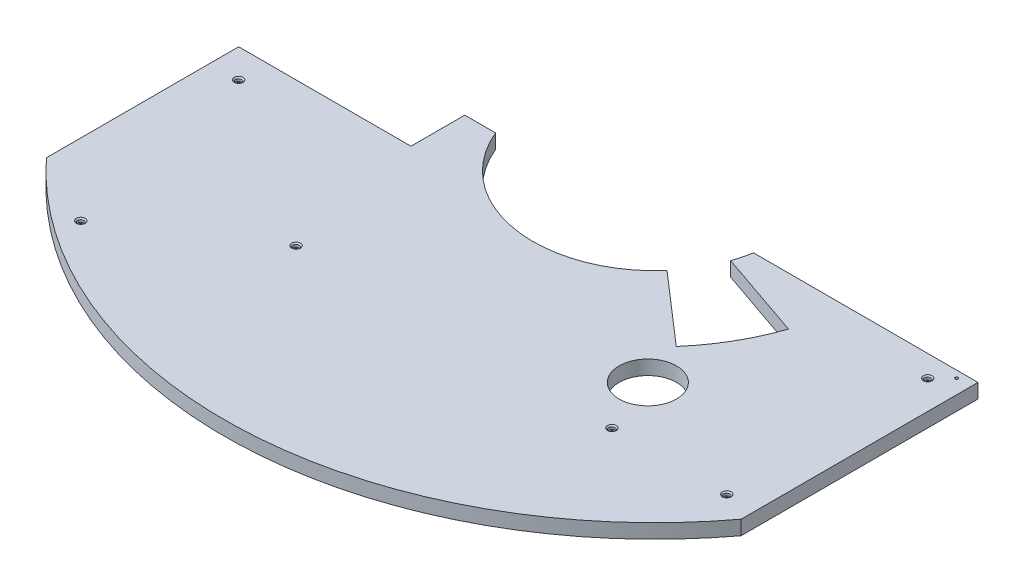
SolidWorks part; units mm, degrees
ref_plane "Front" through (0, 0, 0) normal (0, 0, 1) x (1, 0, 0)
ref_plane "Top" through (0, 0, 0) normal (0, 1, 0) x (1, 0, 0)
ref_plane "Right" through (0, 0, 0) normal (1, 0, 0) x (0, 0, -1)
sketch "Sketch2" plane through (0, 0, 0) normal (0, 1, 0) x (1, 0, 0)
  line L1 (-406.5798, 524.4548) -> (1600.0202, 524.4548)
  line L2 (-406.5798, 524.4548) -> (-406.5798, -237.5452)
  line L3 (-406.5798, -237.5452) -> (1600.0202, -237.5452)
  line L4 (1600.0202, 524.4548) -> (1600.0202, -237.5452)
  dimension "D1" = 762
  dimension "D2" = 2006.6
extrude "Boss-Extrude1" add sketch "Sketch2" along normal blind 25.4
sketch "Sketch102" plane through (0, 25.4, 0) normal (0, 1, 0) x (1, 0, 0)
  line L1 (1600.0202, -237.5452) -> (1600.0202, 524.4548) construction
  line L3 (1600.0202, 524.4548) -> (-406.5798, 524.4548) construction
  line L4 (-101.7798, 851.1379) -> (-101.7798, -458.2879) construction
  line L6 (152.2202, 524.4548) -> (439.7646, 274.4963)
  line L7 (512.4628, 400.4133) -> (152.2202, 524.4548)
  line L9 (-406.5798, 524.4548) -> (1600.0202, 524.4548)
  line L10 (-406.5798, 524.4548) -> (-406.5798, 67.2548)
  line L11 (-406.5798, 67.2548) -> (1600.0202, 67.2548)
  line L12 (1600.0202, 524.4548) -> (1600.0202, 67.2548)
  circle A0 centre (152.2202, 524.4548) radius 215.9
  arc A1 (439.7646, 274.4963) -> (512.4628, 400.4133) centre (152.2202, 524.4548) ccw
  circle A2 centre (469.7202, 194.2548) radius 50.8
  circle A3 centre (152.2202, 524.4548) radius 762
  dimension "D3" = 558.8
  dimension "D4" = 431.8
  dimension "D9" = 101.6
  dimension "D5" = 254
  dimension "D6" = 41
  dimension "D7" = 22
  dimension "D8" = 381
  dimension "D10" = 330.2
  dimension "D11" = 317.5
  dimension "D12" = 457.2
sketch "Sketch113" plane through (0, 25.4, 0) normal (0, 1, 0) x (1, 0, 0)
  line L0 (761.8202, 67.2548) -> (761.8202, 807.6635) construction
  line L1 (-406.5798, 67.2548) -> (1600.0202, 67.2548) construction
  line L2 (-406.5798, 524.4548) -> (1600.0202, 524.4548) construction
  line L3 (736.4202, 807.6635) -> (736.4202, -32.6479) construction
  line L4 (807.5255, 473.6548) -> (-505.9709, 473.6548) construction
  circle A0 centre (152.2202, 524.4548) radius 762 construction
  dimension "D1" = 25.4
  dimension "D2" = 50.8
sketch "Sketch120" plane through (0, 25.4, 0) normal (0, 1, 0) x (1, 0, 0)
  line L0 (-406.5798, 524.4548) -> (1600.0202, 524.4548) construction
  line L1 (364.7319, 486.3548) -> (761.8202, 486.3548)
  line L2 (761.8202, 67.2548) -> (761.8202, 807.6635) construction
  line L3 (761.8202, 486.3548) -> (761.8202, 524.4548)
  line L4 (761.8202, 524.4548) -> (368.1202, 524.4548)
  arc A0 (368.1202, 524.4548) -> (364.7319, 486.3548) centre (152.2202, 524.4548) cw
  circle A1 centre (152.2202, 524.4548) radius 215.9 construction
  dimension "D1" = 38.1
extrude "Cut-Extrude18" cut sketch "Sketch120" against normal through all
hole_wizard "1/4-20 Tapped Hole1" positions "Sketch122" profile "Sketch121" tap size "1/4-20" standard "ANSI Inch" end condition through all
sketch "Sketch122" plane through (0, 25.4, 0) normal (0, 1, 0) x (1, 0, 0)
  line L0 (736.4202, 807.6635) -> (736.4202, -32.6479) construction
  point P0 (736.4202, 473.9488)
sketch "Sketch121" plane through (736.4202, 25.4, -473.9488) normal (1, 0, 0) x (0, 0, 1)
  line L0 (0, 0) -> (0, 25.4)
  line L1 (0, 25.4) -> (2.5527, 25.4)
  line L2 (2.5527, 25.4) -> (2.5527, 0)
  line L5 (2.5527, 0) -> (0, 0)
  line L11 (0, -6.35) -> (0, 107.95) construction
  dimension "Thru Tap Drill Dia." = 5.1054
  dimension "Thru Tap Drill Depth" = 25.4
cosmetic thread "Hole Thread1" parameters "D2"=6.35
pattern_linear "LPattern1" [suppressed] count 45 spacing 25.4 along (-1, 0, 0) count 28 spacing 25.4 along (0, 0, 1)
sketch "Sketch4" plane through (0, 25.4, 0) normal (0, 1, 0) x (1, 0, 0)
  line L0 (1600.0202, 524.4548) -> (761.8202, 524.4548) construction
  circle A0 centre (152.2202, 524.4548) radius 215.9
  circle A1 centre (152.2202, 524.4548) radius 215.9 construction
  dimension "D1" = 0
  dimension "D2" = 431.8
extrude "Cut-Extrude1" cut sketch "Sketch4" against normal through all
sketch "Assembly Ref." plane through (0, 0, 0) normal (0, -1, 0) x (1, 0, 0)
  line L0 (-323.2678, -1076.4559) -> (-323.2678, 602.6054) construction
  line L1 (76.0202, -600.6548) -> (228.4202, -600.6548)
  line L2 (76.0202, -600.6548) -> (76.0202, -448.2548)
  line L3 (76.0202, -448.2548) -> (228.4202, -448.2548)
  line L4 (228.4202, -600.6548) -> (228.4202, -448.2548)
  line L5 (76.0202, -600.6548) -> (228.4202, -448.2548) construction
  line L6 (76.0202, -448.2548) -> (228.4202, -600.6548) construction
  line L7 (-711.3798, -676.8548) -> (431.6202, -676.8548)
  line L8 (-711.3798, -676.8548) -> (-711.3798, -372.0548)
  line L9 (-711.3798, -372.0548) -> (431.6202, -372.0548)
  line L10 (431.6202, -676.8548) -> (431.6202, -372.0548)
  line L12 (-779.2323, -1108.6548) -> (1769.2025, -1108.6548)
  line L13 (-779.2323, -1108.6548) -> (-779.2323, 85.1452)
  line L14 (-779.2323, 85.1452) -> (1769.2025, 85.1452)
  line L15 (1769.2025, -1108.6548) -> (1769.2025, 85.1452)
  line L16 (533.2202, -981.6548) -> (-76.3798, -981.6548)
  line L17 (533.2202, -981.6548) -> (533.2202, -67.2548)
  line L18 (533.2202, -67.2548) -> (-76.3798, -67.2548)
  line L19 (-76.3798, -981.6548) -> (-76.3798, -67.2548)
  point P0 (152.2202, -524.4548)
  dimension "D1" = 152.4
  dimension "D2" = 152.4
  dimension "D3" = 304.8
  dimension "D4" = 152.4
  dimension "D5" = 279.4
  dimension "D6" = 1143
  dimension "D7" = 475.488
  dimension "D8" = 1193.8
  dimension "D9" = 609.6
  dimension "D10" = 609.6
  dimension "D11" = 914.4
  dimension "D12" = 228.6
  dimension "D13" = 457.2
sketch "Sketch24" plane through (0, 25.4, 0) normal (0, 1, 0) x (1, 0, 0)
  circle A0 centre (76.0202, 448.2548) radius 25.4
  circle A1 centre (228.4202, 448.2548) radius 25.4
  dimension "D1" = 50.8
  dimension "D2" = 50.8
sketch "Sketch26" plane through (0, 25.4, 0) normal (0, 1, 0) x (1, 0, 0)
  line L1 (-406.5798, 524.4548) -> (-25.5798, 524.4548)
  line L2 (-406.5798, 524.4548) -> (-406.5798, 441.9048)
  line L3 (-406.5798, 441.9048) -> (-25.5798, 441.9048)
  line L4 (-25.5798, 524.4548) -> (-25.5798, 441.9048)
  dimension "D1" = 82.55
  dimension "D2" = 381
extrude "Cut-Extrude2" cut sketch "Sketch26" against normal through all
sketch "Sketch109" plane through (0, 25.4, 0) normal (0, 1, 0) x (1, 0, 0)
  circle A0 centre (469.7202, 194.2548) radius 50.8
extrude "Cut-Extrude15" cut sketch "Sketch109" against normal through all
sketch "Sketch48" plane through (0, 25.4, 0) normal (0, 1, 0) x (1, 0, 0)
  line L0 (1600.0202, 524.4548) -> (761.8202, 524.4548) construction
  line L1 (-101.7798, 346.6548) -> (-406.5798, 346.6548)
  line L2 (-101.7798, 346.6548) -> (-101.7798, 441.9048)
  line L3 (-101.7798, 441.9048) -> (-406.5798, 441.9048)
  line L4 (-406.5798, 346.6548) -> (-406.5798, 441.9048)
  dimension "D1" = 177.8
  dimension "D2" = 254
extrude "Cut-Extrude9" cut sketch "Sketch48" against normal through all
sketch "Sketch56" plane through (0, 25.4, 0) normal (0, 1, 0) x (1, 0, 0)
  line L0 (512.4628, 400.4133) -> (152.2202, 524.4548)
  line L1 (152.2202, 524.4548) -> (439.7646, 274.4963)
  line L2 (1600.0202, 524.4548) -> (761.8202, 524.4548) construction
  arc A0 (439.7646, 274.4963) -> (512.4628, 400.4133) centre (152.2202, 524.4548) ccw
  dimension "D2" = 22
  dimension "D3" = 381
  dimension "D1" = 41
extrude "Cut-Extrude12" cut sketch "Sketch56" against normal through all
sketch "Sketch57" plane through (0, 0, 0) normal (0, -1, 0) x (-1, 0, 0)
  line L0 (-152.2202, 524.4548) -> (-343.7367, 249.6263) construction
  circle A0 centre (-352.084, 360.9632) radius 34.5442
  circle A1 centre (-342.2371, 410.6424) radius 18.1483
sketch "Sketch105" plane through (0, 25.4, 0) normal (0, 1, 0) x (1, 0, 0)
  line L0 (-406.5798, 346.6548) -> (-406.5798, -237.5452) construction
  line L1 (152.2202, -237.5452) -> (-406.5798, -237.5452)
  line L2 (-406.5798, -237.5452) -> (-406.5798, 6.3944)
  arc A0 (-406.5798, 6.3944) -> (152.2202, -237.5452) centre (152.2202, 524.4548) ccw
  circle A1 centre (152.2202, 524.4548) radius 762 construction
extrude "Cut-Extrude13" cut sketch "Sketch105" against normal through all
sketch "Sketch111" plane through (0, 25.4, 0) normal (0, 1, 0) x (1, 0, 0)
  line L0 (-406.5798, 67.2548) -> (1600.0202, 67.2548) construction
  line L1 (761.8202, 67.2548) -> (761.8202, 524.4548)
  line L2 (-406.5798, 524.4548) -> (1600.0202, 524.4548) construction
  line L3 (761.8202, 524.4548) -> (1600.0202, 524.4548)
  line L4 (1600.0202, 524.4548) -> (1600.0202, -237.5452)
  line L5 (1600.0202, -237.5452) -> (152.2202, -237.5452)
  arc A0 (152.2202, -237.5452) -> (761.8202, 67.2548) centre (152.2202, 524.4548) ccw
extrude "Cut-Extrude17" cut sketch "Sketch111" against normal through all
hole_wizard "CBORE for 1/4 Socket Head Cap Screw1" positions "Sketch124" profile "Sketch123" counterbore size "1/4" standard "ANSI Inch" end condition through all
sketch "Sketch124" plane through (0, 25.4, 0) normal (0, 1, 0) x (1, 0, 0)
  line L0 (-406.5798, 67.2548) -> (1600.0202, 67.2548) construction
  line L1 (-76.3798, 981.6548) -> (-76.3798, 67.2548) construction
  line L2 (533.2202, 981.6548) -> (533.2202, 67.2548) construction
  line L3 (-406.5798, 346.6548) -> (-101.7798, 346.6548) construction
  line L4 (-406.5798, 524.4548) -> (-406.5798, 67.2548) construction
  line L6 (-779.2323, -85.1452) -> (1769.2025, -85.1452) construction
  line L7 (-406.5798, 346.6548) -> (-406.5798, 6.3944) construction
  line L8 (761.8202, 67.2548) -> (761.8202, 807.6635) construction
  line L9 (364.7319, 486.3548) -> (761.8202, 486.3548) construction
  point P0 (-50.9798, 92.6548)
  point P2 (507.8202, 92.6548)
  point P4 (-355.7798, 295.8548)
  point P6 (-279.5798, -59.7452)
  point P8 (711.0202, 448.2548)
  point P10 (711.0202, 92.6548)
  dimension "D1" = 25.4
  dimension "D2" = 25.4
  dimension "D3" = 25.4
  dimension "D4" = 25.4
  dimension "D5" = 50.8
  dimension "D6" = 50.8
  dimension "D7" = 127
  dimension "D8" = 25.4
  dimension "D9" = 50.8
  dimension "D10" = 38.1
  dimension "D11" = 25.4
  dimension "D12" = 50.8
sketch "Sketch123" plane through (-50.9798, 25.4, -92.6548) normal (1, 0, 0) x (0, 0, 1)
  line L0 (0, 0) -> (0, 25.4)
  line L1 (0, 25.4) -> (3.3782, 25.4)
  line L3 (3.3782, 25.4) -> (3.3782, 6.35)
  line L4 (5.5562, 6.35) -> (3.3782, 6.35)
  line L5 (5.5562, 6.35) -> (5.5562, 2.2225)
  line L6 (5.5562, 2.2225) -> (7.7788, 0)
  line L7 (7.7788, 0) -> (0, 0)
  line L8 (-5.5562, 2.2225) -> (-7.7788, 0) construction
  line L11 (0, -6.35) -> (0, 107.95) construction
  dimension "Thru Hole Dia." = 6.7564
  dimension "Thru Hole Depth" = 25.4
  dimension "C'Bore Dia." = 11.1125
  dimension "C'Bore Depth" = 6.35
  dimension "Near C'Sink Dia." = 15.5575
  dimension "Near C'Sink Angle" = 90
